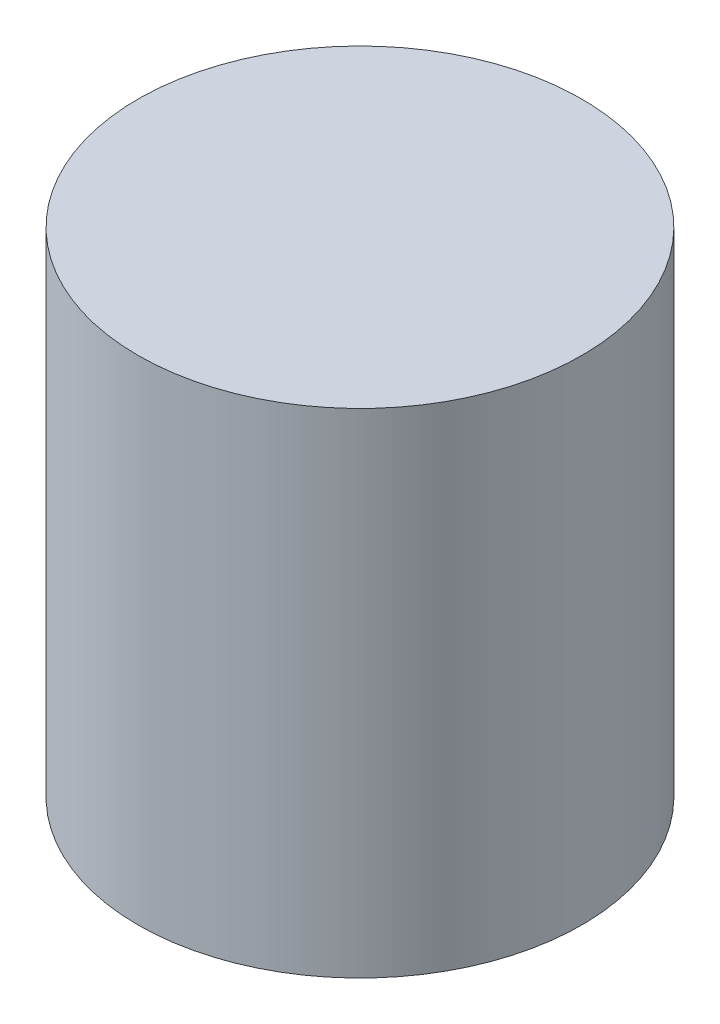
SolidWorks part; units mm, degrees
ref_plane "Front Plane" through (0, 0, 0) normal (0, 0, 1) x (1, 0, 0)
ref_plane "Top Plane" through (0, 0, 0) normal (0, 1, 0) x (1, 0, 0)
ref_plane "Right Plane" through (0, 0, 0) normal (1, 0, 0) x (0, 0, -1)
sketch "Sketch1" plane through (0, 0, 0) normal (0, 1, 0) x (1, 0, 0)
  circle A0 centre (0, 0) radius 2.25
  dimension "D1" = 4.5
extrude "Boss-Extrude1" add sketch "Sketch1" along normal blind 5
